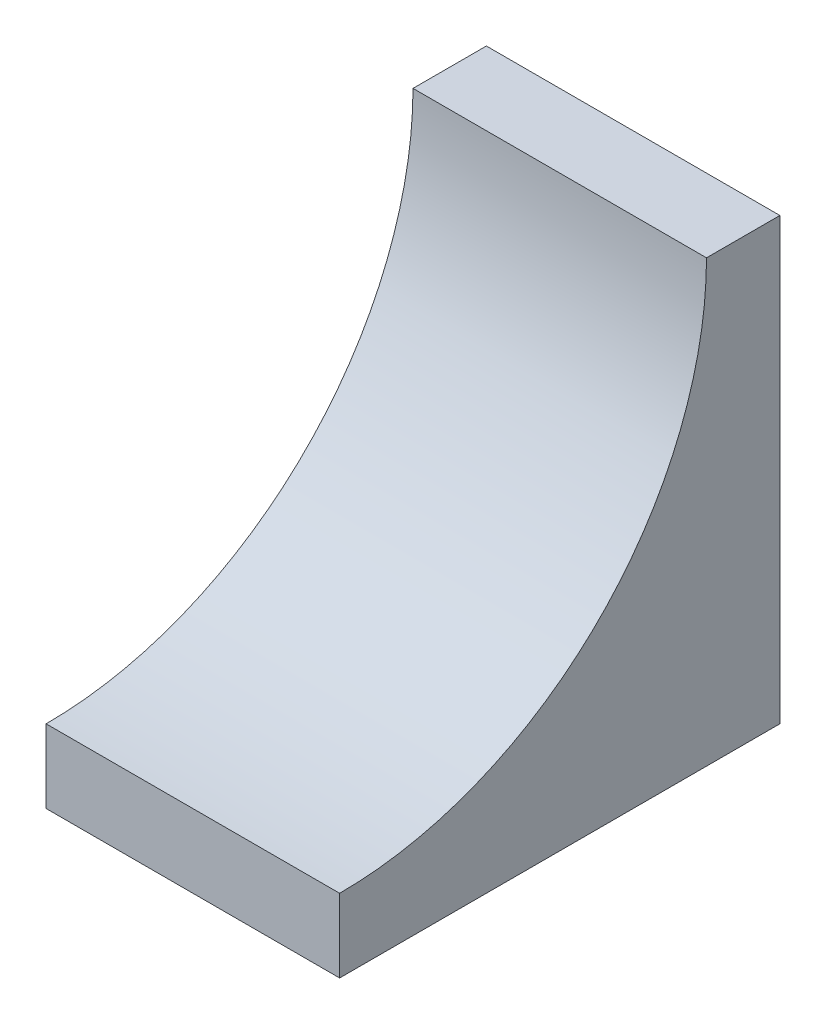
SolidWorks part; units mm, degrees
material "PVC Rigid"
ref_plane "Front Plane" through (0, 0, 0) normal (0, 0, 1) x (1, 0, 0)
ref_plane "Top Plane" through (0, 0, 0) normal (0, 1, 0) x (1, 0, 0)
ref_plane "Right Plane" through (0, 0, 0) normal (1, 0, 0) x (0, 0, -1)
sketch "Sketch1" plane through (0, 0, 0) normal (1, 0, 0) x (0, 0, -1)
  line L0 (0, 0) -> (0, 19.05)
  line L1 (0, 19.05) -> (-3.175, 19.05)
  line L2 (-19.05, 3.175) -> (-19.05, 0)
  line L3 (-19.05, 0) -> (0, 0)
  arc A0 (-3.175, 19.05) -> (-19.05, 3.175) centre (-19.05, 19.05) cw
  point P6 (-19.05, 19.05)
  point P8 (0, 0)
  point P9 (0, 0)
  dimension "D1" = 19.05
  dimension "D2" = 3.175
extrude "Boss-Extrude1" add sketch "Sketch1" along normal mid plane 12.7 contours L1 A0 L2 L3 L0
